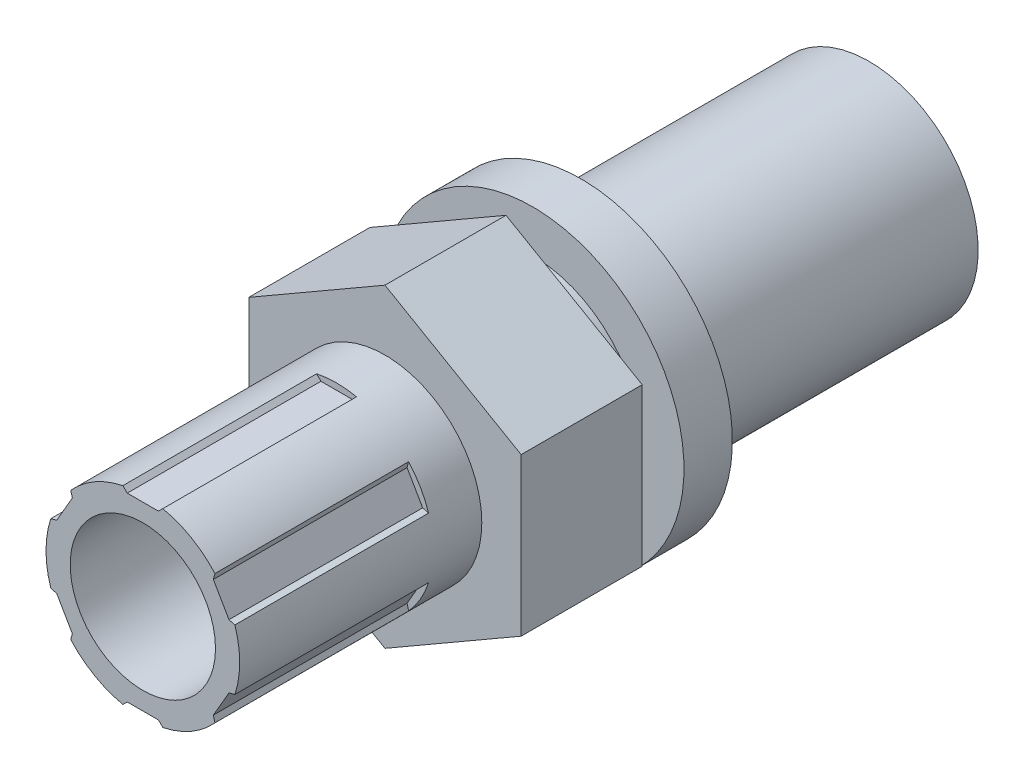
SolidWorks part; units mm, degrees
material "Alloy Steel"
ref_plane "Front Plane" through (0, 0, 0) normal (0, 0, 1) x (1, 0, 0)
ref_plane "Top Plane" through (0, 0, 0) normal (0, 1, 0) x (1, 0, 0)
ref_plane "Right Plane" through (0, 0, 0) normal (1, 0, 0) x (0, 0, -1)
sketch "Sketch1" plane through (0, 0, 0) normal (0, 0, 1) x (1, 0, 0)
  line L2 (0, 8.2489) -> (-7.1437, 4.1244)
  line L3 (-7.1437, 4.1244) -> (-7.1437, -4.1244)
  line L4 (-7.1437, -4.1244) -> (0, -8.2489)
  line L5 (0, -8.2489) -> (7.1438, -4.1244)
  line L6 (7.1438, -4.1244) -> (7.1438, 4.1244)
  line L7 (7.1438, 4.1244) -> (0, 8.2489)
  circle A0 centre (0, 0) radius 7.1437 construction
  dimension "D1" = 14.2875
extrude "Boss-Extrude1" add sketch "Sketch1" along normal blind 6.35
sketch "Sketch2" plane through (0, 0, 6.35) normal (0, 0, 1) x (1, 0, 0)
  circle A0 centre (0, 0) radius 3.81
  circle A1 centre (0, 0) radius 5.08
  dimension "D1" = 7.62
  dimension "D2" = 10.16
extrude "Boss-Extrude2" add sketch "Sketch2" along normal blind 12.7
sketch "Sketch3" plane through (0, 0, 0) normal (0, 0, -1) x (-1, 0, 0)
  circle A0 centre (0, 0) radius 5.715
  dimension "D1" = 11.43
extrude "Boss-Extrude3" add sketch "Sketch3" along normal blind 19.05
ref_plane "Plane1" through (0, 0, -1.397) normal (0, 0, -1) x (-1, 0, 0)
sketch "Sketch4" plane through (0, 0, -1.397) normal (0, 0, -1) x (-1, 0, 0)
  circle A0 centre (0, 0) radius 7.9372
extrude "Boss-Extrude4" add sketch "Sketch4" along normal blind 2.54
sketch "Sketch5" plane through (0, 0, 6.35) normal (0, 0, 1) x (1, 0, 0)
  circle A0 centre (0, 0) radius 3.81
extrude "Cut-Extrude1" cut sketch "Sketch5" against normal through all
sketch "Sketch6" plane through (0, 0, 19.05) normal (0, 0, 1) x (1, 0, 0)
  line L0 (-0.8187, 4.7439) -> (0.8187, 4.7439)
  line L1 (0.8187, 4.7439) -> (1.27, 5.1953)
  line L2 (1.27, 5.1953) -> (-1.27, 5.1953)
  line L3 (0, 5.1953) -> (0, 4.7439) construction
  line L4 (-0.8187, 4.7439) -> (-1.27, 5.1953)
  dimension "D1" = 2.54
extrude "Cut-Extrude2" cut sketch "Sketch6" against normal blind 10.16
pattern_circular "CirPattern1" count 6 over 360 about axis through (0, 0, 0) along (0, 0, 1) of "Cut-Extrude2"
